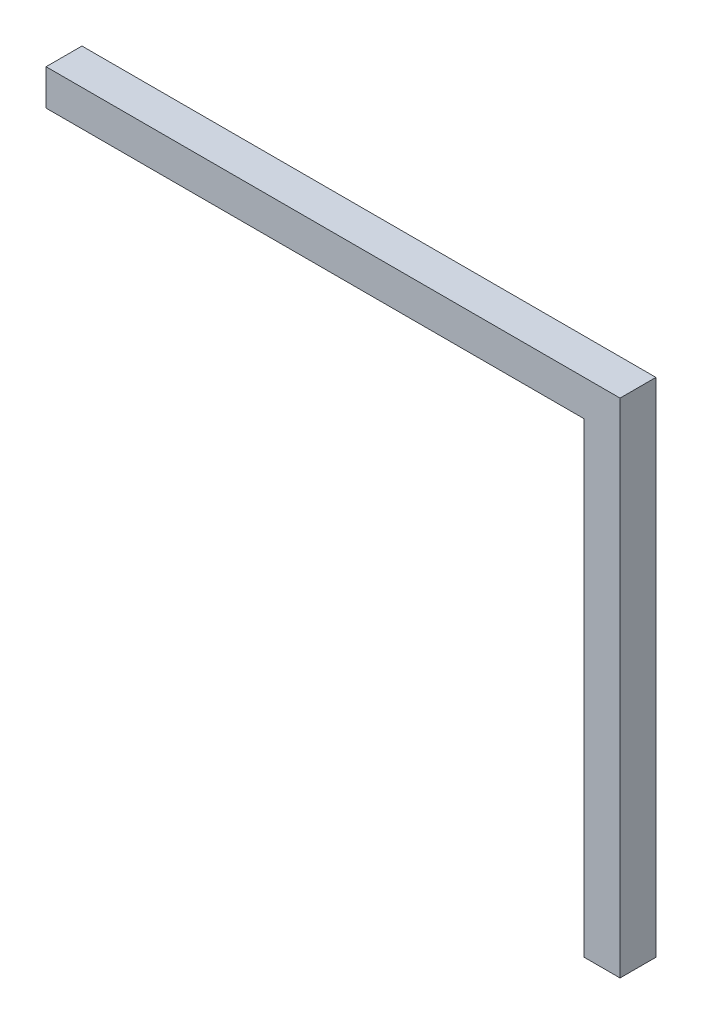
SolidWorks part; units mm, degrees
ref_plane "Front" through (0, 0, 0) normal (0, 0, 1) x (1, 0, 0)
ref_plane "Top" through (0, 0, 0) normal (0, 1, 0) x (1, 0, 0)
ref_plane "Right" through (0, 0, 0) normal (1, 0, 0) x (0, 0, -1)
sketch "Sketch1" plane through (0, 0, 0) normal (0, 0, 1) x (1, 0, 0)
  line L0 (-13.2, 17.5626) -> (-13.2, 17.0626)
  line L1 (-13.2, 17.5626) -> (-5.2, 17.5626)
  line L2 (-13.2, 17.5626) -> (-13.2, 17.0626)
  line L3 (-5.7, 10.5626) -> (-5.2, 10.5626)
  line L4 (-5.2, 17.5626) -> (-5.2, 10.5626)
  line L7 (-13.2, 17.0626) -> (-5.7, 17.0626)
  line L9 (-5.2, 10.5626) -> (-5.7, 10.5626)
  line L10 (-5.7, 10.5626) -> (-5.7, 17.0626)
  point P4 (16.4765, -3.1811)
  point P7 (-5.9, 12.926)
  dimension "D1" = 0.5
  dimension "D2" = 0.5
  dimension "D3" = 7
  dimension "D4" = 8
extrude "Boss-Extrude1" add sketch "Sketch1" along normal blind 0.5 contours L10 L3 L4 L1 L0 L7
